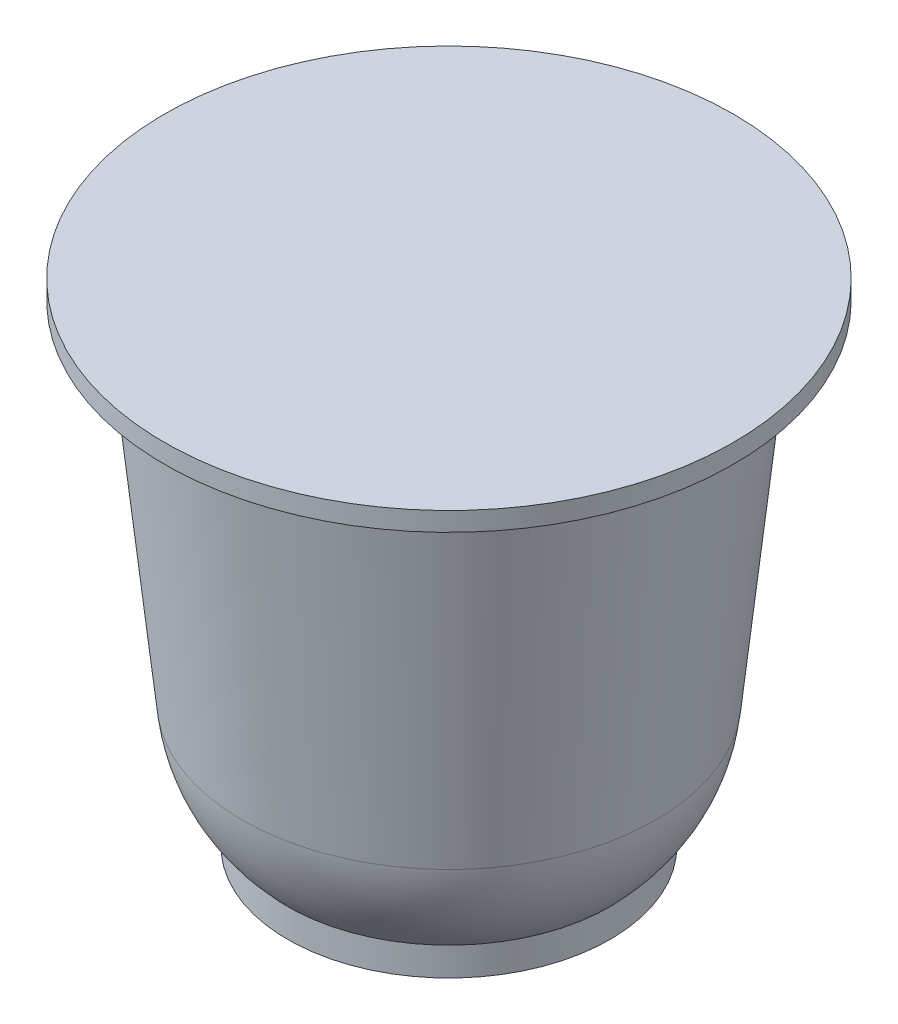
SolidWorks part; units mm, degrees
ref_plane "Front Plane" through (0, 0, 0) normal (0, 0, 1) x (1, 0, 0)
ref_plane "Top Plane" through (0, 0, 0) normal (0, 1, 0) x (1, 0, 0)
ref_plane "Right Plane" through (0, 0, 0) normal (1, 0, 0) x (0, 0, -1)
sketch "Sketch1" plane through (0, 0, 0) normal (0, 0, 1) x (1, 0, 0)
  line L0 (0, 0) -> (0, 26.3652)
  line L1 (0, -55) -> (0, 55) construction
  line L2 (0, 26.3652) -> (15.24, 26.3652)
  line L3 (0, 0) -> (8.636, 0)
  line L4 (8.636, 0) -> (8.636, 1.5235)
  line L5 (15.24, 26.3652) -> (15.24, 25.3492)
  line L6 (15.24, 25.3492) -> (13.0114, 25.3492)
  line L7 (13.0114, 25.3492) -> (11.0715, 6.7577)
  arc A0 (11.0715, 6.7577) -> (8.636, 1.5235) centre (2.251, 7.6781) cw
  dimension "D4" = 1.016
  dimension "D1" = 26.3652
  dimension "D2" = 15.24
  dimension "D3" = 8.636
revolve "Revolve1" add sketch "Sketch1" angle 360 about L0
